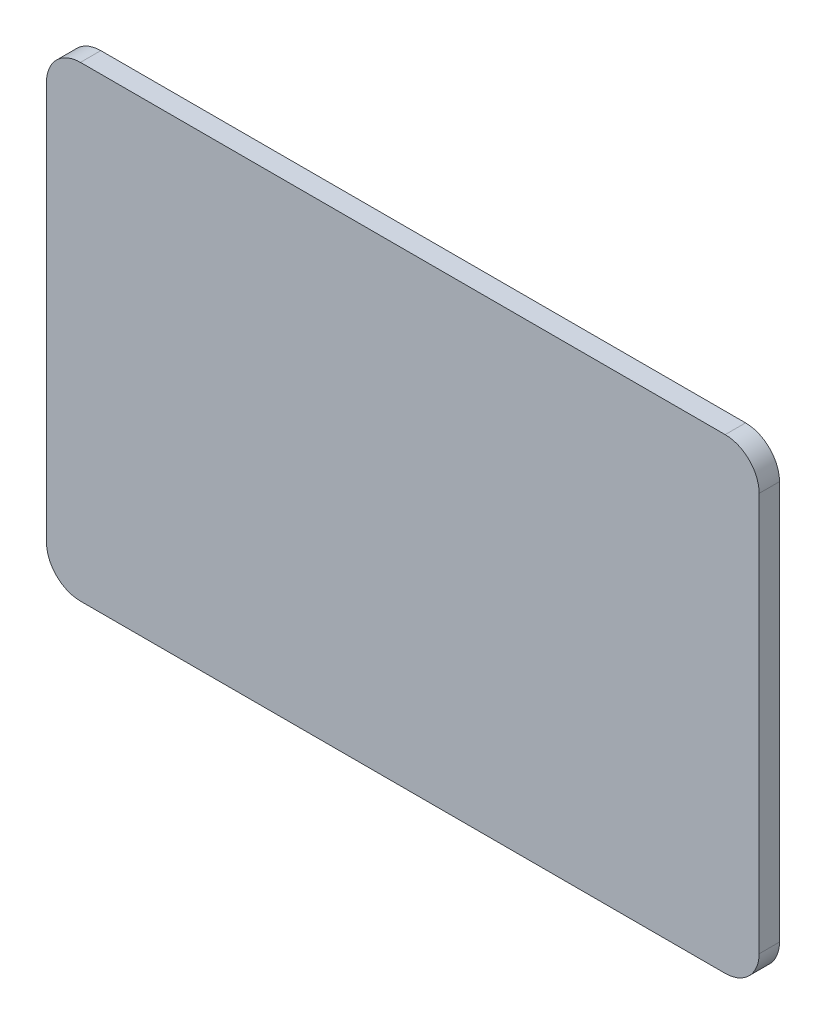
SolidWorks part; units mm, degrees
ref_plane "Front Plane" through (0, 0, 0) normal (0, 0, 1) x (1, 0, 0)
ref_plane "Top Plane" through (0, 0, 0) normal (0, 1, 0) x (1, 0, 0)
ref_plane "Right Plane" through (0, 0, 0) normal (1, 0, 0) x (0, 0, -1)
sketch "Sketch1" plane through (0, 0, 0) normal (0, 0, 1) x (1, 0, 0)
  line L1 (47.5, -34.375) -> (-47.5, -34.375)
  line L2 (52.5, -29.375) -> (52.5, 29.375)
  line L3 (47.5, 34.375) -> (-47.5, 34.375)
  line L4 (-52.5, -29.375) -> (-52.5, 29.375)
  arc A0 (-47.5, -34.375) -> (-52.5, -29.375) centre (-47.5, -29.375) cw
  arc A1 (47.5, -34.375) -> (52.5, -29.375) centre (47.5, -29.375) ccw
  arc A2 (52.5, 29.375) -> (47.5, 34.375) centre (47.5, 29.375) ccw
  arc A3 (-47.5, 34.375) -> (-52.5, 29.375) centre (-47.5, 29.375) ccw
  point P0 (0, 0)
  point P8 (-52.5, -34.375)
  point P13 (52.5, 34.375)
  point P16 (-52.5, 34.375)
  dimension "D3" = 5
  dimension "D1" = 105
  dimension "D2" = 68.75
extrude "Boss-Extrude1" add sketch "Sketch1" along normal blind 3
